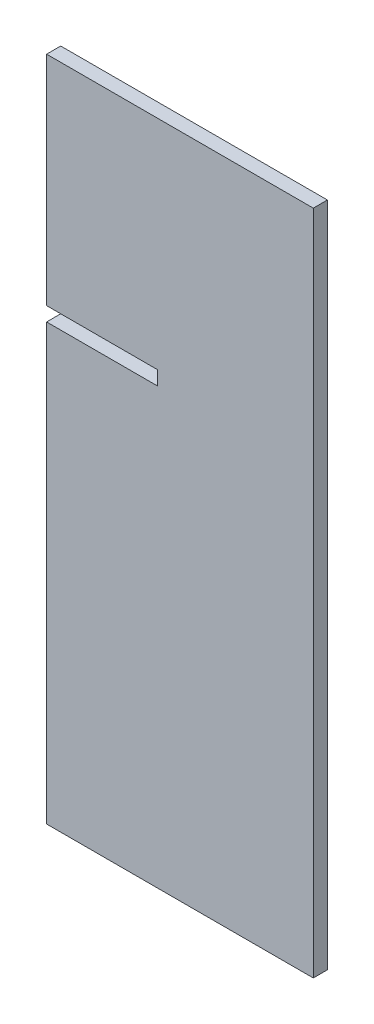
SolidWorks part; units mm, degrees
material "FiberBoard"
ref_plane "Front Plane" through (0, 0, 0) normal (0, 0, 1) x (1, 0, 0)
ref_plane "Top Plane" through (0, 0, 0) normal (0, 1, 0) x (1, 0, 0)
ref_plane "Right Plane" through (0, 0, 0) normal (1, 0, 0) x (0, 0, -1)
sketch "Sketch1" plane through (0, 0, 0) normal (0, 0, 1) x (1, 0, 0)
  line L1 (-30, 75) -> (30, 75)
  line L2 (-30, 75) -> (-30, -75)
  line L3 (-30, -75) -> (30, -75)
  line L4 (30, 75) -> (30, -75)
  line L5 (-30, 75) -> (30, -75) construction
  line L6 (-30, -75) -> (30, 75) construction
  point P0 (0, 0)
  dimension "D1" = 60
  dimension "D2" = 150
extrude "Boss-Extrude1" add sketch "Sketch1" along normal blind 3.175
sketch "Sketch2" plane through (0, 0, 3.175) normal (0, 0, 1) x (1, 0, 0)
  line L0 (-30, 75) -> (-30, -75) construction
  line L5 (30, -75) -> (30, 75) construction
  line L14 (-30, 75) -> (30, 75) construction
  line L19 (-30, -75) -> (30, -75) construction
  line L29 (-30, 26) -> (-5, 26)
  line L30 (-30, 26) -> (-30, 22.825)
  line L31 (-30, 22.825) -> (-5, 22.825)
  line L32 (-5, 26) -> (-5, 22.825)
  line L33 (30, 26) -> (5, 26) construction
  line L34 (30, 26) -> (30, 22.825) construction
  line L35 (30, 22.825) -> (5, 22.825) construction
  line L36 (5, 26) -> (5, 22.825) construction
  dimension "D1" = 25
  dimension "D2" = 3.175
  dimension "D3" = 150
  dimension "D4" = 49
extrude "Cut-Extrude1" cut sketch "Sketch2" against normal blind 3.175
